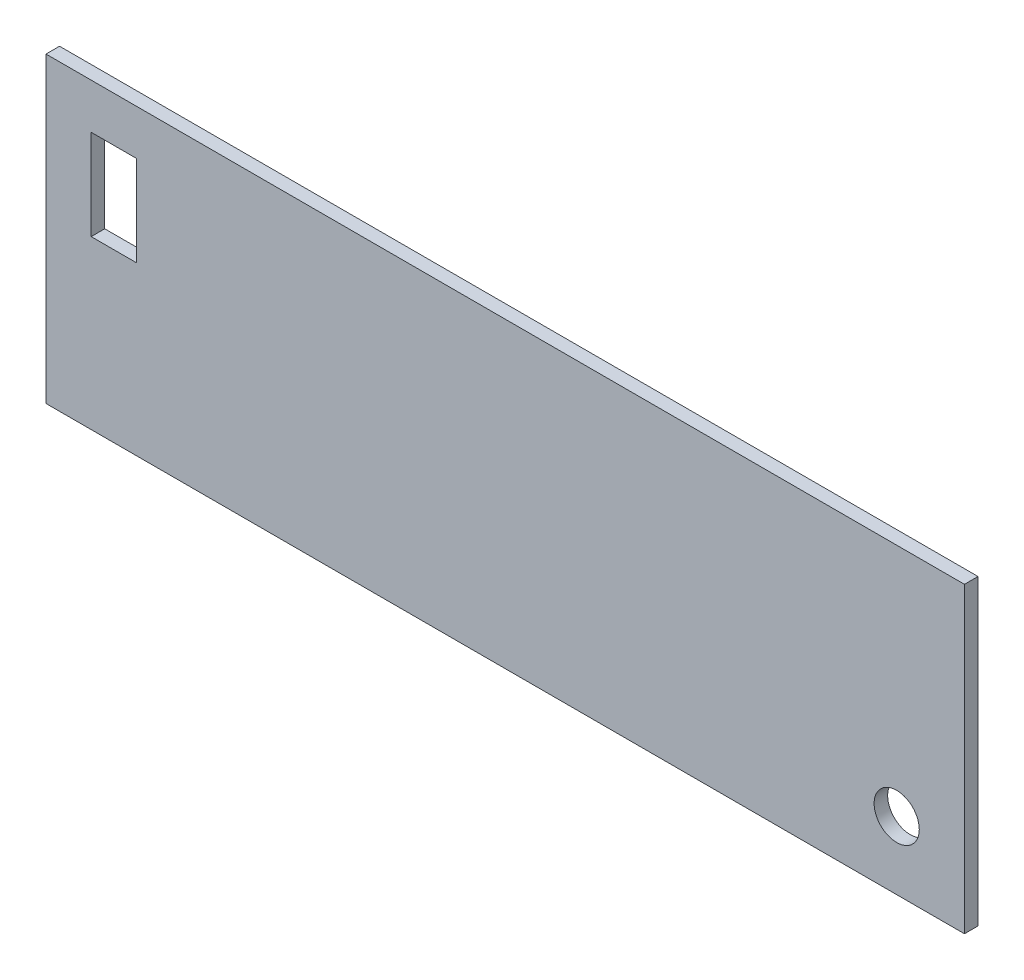
SolidWorks part; units mm, degrees
material "Haya"
ref_plane "Alzado" through (0, 0, 0) normal (0, 0, 1) x (1, 0, 0)
ref_plane "Planta" through (0, 0, 0) normal (0, 1, 0) x (1, 0, 0)
ref_plane "Vista lateral" through (0, 0, 0) normal (1, 0, 0) x (0, 0, -1)
sketch "Croquis1" plane through (0, 0, 0) normal (0, 0, 1) x (1, 0, 0)
  line L1 (-101.655, -33.5) -> (101.655, -33.5)
  line L2 (-101.655, -33.5) -> (-101.655, 33.5)
  line L3 (-101.655, 33.5) -> (101.655, 33.5)
  line L4 (101.655, -33.5) -> (101.655, 33.5)
  line L5 (-101.655, -33.5) -> (101.655, 33.5) construction
  line L6 (-101.655, 33.5) -> (101.655, -33.5) construction
  point P0 (0, 0)
  dimension "D1" = 67
  dimension "D2" = 203.31
extrude "Saliente-Extruir1" add sketch "Croquis1" against normal blind 3
sketch "Croquis2" plane through (0, 0, 0) normal (0, 0, 1) x (1, 0, 0)
  line L2 (101.655, 33.5) -> (-101.655, 33.5) construction
  line L3 (-91.655, 3.5) -> (-81.655, 3.5)
  line L4 (-91.655, 3.5) -> (-91.655, 23.5)
  line L5 (-91.655, 23.5) -> (-81.655, 23.5)
  line L6 (-81.655, 3.5) -> (-81.655, 23.5)
  line L7 (-91.655, 3.5) -> (-81.655, 23.5) construction
  line L8 (-91.655, 23.5) -> (-81.655, 3.5) construction
  line L10 (-101.655, 33.5) -> (-101.655, -33.5) construction
  point P0 (-86.655, 13.5)
  dimension "D1" = 10
  dimension "D2" = 20
  dimension "D3" = 20
  dimension "D4" = 15
extrude "Cortar-Extruir1" cut sketch "Croquis2" against normal up to next
sketch "Croquis3" plane through (0, 0, 0) normal (0, 0, 1) x (1, 0, 0)
  line L0 (-101.655, -33.5) -> (101.655, -33.5) construction
  line L1 (101.655, -33.5) -> (101.655, 33.5) construction
  circle A0 centre (86.655, -18.5) radius 5
  dimension "D1" = 10
  dimension "D2" = 15
  dimension "D3" = 15
extrude "Cortar-Extruir2" cut sketch "Croquis3" against normal up to next
